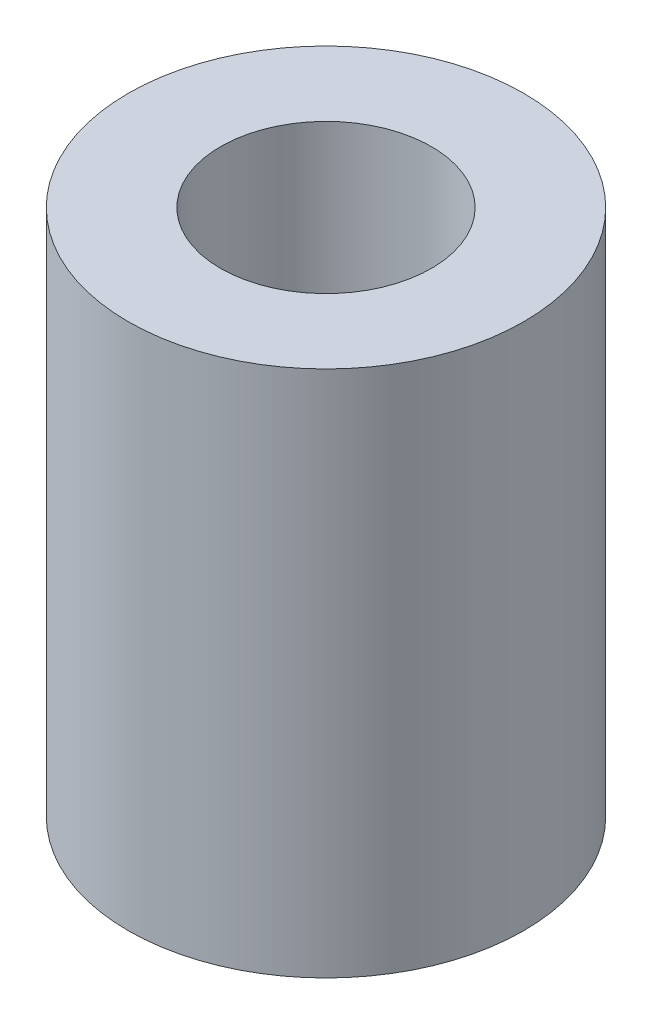
SolidWorks part; units mm, degrees
material "policarbonato"
ref_plane "Alzado" through (0, 0, 0) normal (0, 0, 1) x (1, 0, 0)
ref_plane "Planta" through (0, 0, 0) normal (0, 1, 0) x (1, 0, 0)
ref_plane "Vista lateral" through (0, 0, 0) normal (1, 0, 0) x (0, 0, -1)
sketch "Sketch1" plane through (0, 0, 0) normal (0, 1, 0) x (1, 0, 0)
  circle A0 centre (0, 0) radius 1.6
  circle A1 centre (0, 0) radius 3
  dimension "D1" = 3.2
  dimension "D2" = 6
extrude "Boss-Extrude1" add sketch "Sketch1" along normal blind 8
